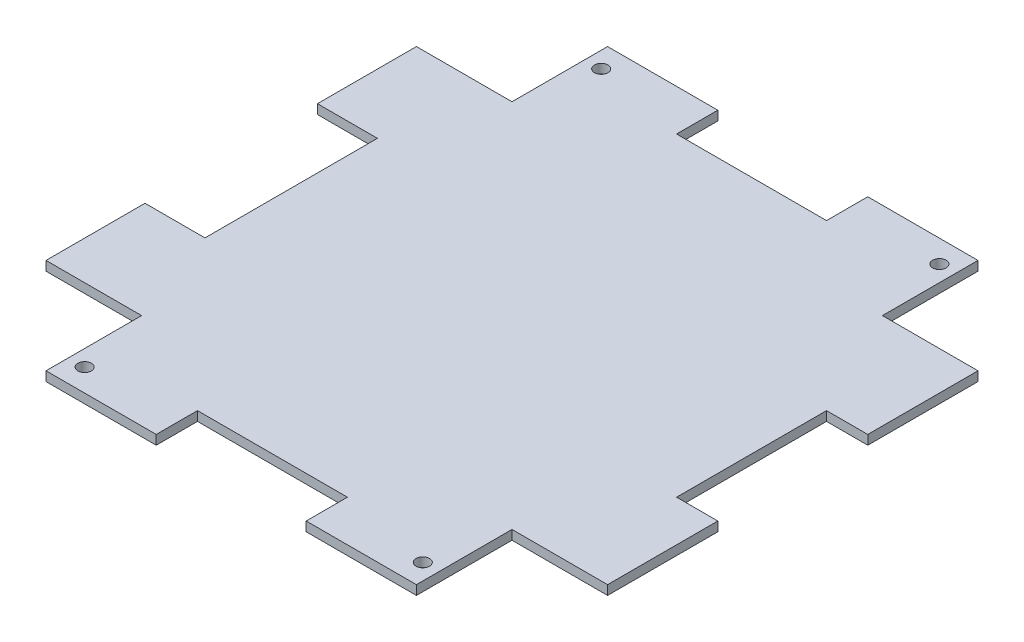
SolidWorks part; units mm, degrees
ref_plane "Front Plane" through (0, 0, 0) normal (0, 0, 1) x (1, 0, 0)
ref_plane "Top Plane" through (0, 0, 0) normal (0, 1, 0) x (1, 0, 0)
ref_plane "Right Plane" through (0, 0, 0) normal (1, 0, 0) x (0, 0, -1)
sketch "Sketch1" plane through (0, 0, 0) normal (0, 1, 0) x (1, 0, 0)
  line L0 (-62.2282, -68.317) -> (-29.8462, -68.317)
  line L1 (-29.8462, -68.317) -> (-29.8462, -100.699)
  line L2 (-29.8462, -100.699) -> (95.6398, -100.699)
  line L3 (95.6398, -100.699) -> (95.6398, -68.317)
  line L4 (95.6398, -68.317) -> (128.0218, -68.317)
  line L5 (128.0218, -68.317) -> (128.0218, 57.169)
  line L6 (128.0218, 57.169) -> (95.6398, 57.169)
  line L7 (95.6398, 57.169) -> (95.6398, 89.551)
  line L8 (95.6398, 89.551) -> (-29.8462, 89.551)
  line L9 (-29.8462, 89.551) -> (-29.8462, 57.169)
  line L10 (-29.8462, 57.169) -> (-62.2282, 57.169)
  line L11 (-62.2282, 57.169) -> (-62.2282, -68.317)
  dimension "D1" = 32.382
  dimension "D2" = 190.25
  dimension "D3" = 190.25
extrude "Boss-Extrude1" add sketch "Sketch1" along normal blind 3.175
sketch "Sketch2" plane through (0, 3.175, 0) normal (0, 1, 0) x (1, 0, 0)
  line L0 (-29.8462, -100.699) -> (95.6398, -100.699) construction
  line L1 (-29.8462, -68.317) -> (-29.8462, -100.699) construction
  line L2 (95.6398, 89.551) -> (-29.8462, 89.551) construction
  line L3 (95.6398, 57.169) -> (95.6398, 89.551) construction
  circle A0 centre (-24.3852, 81.931) radius 2.286
  circle A1 centre (90.1788, 81.931) radius 2.286
  circle A2 centre (90.1788, -93.079) radius 2.286
  circle A3 centre (-24.3852, -93.079) radius 2.286
  dimension "D1" = 4.572
  dimension "D2" = 7.62
  dimension "D3" = 5.461
  dimension "D4" = 7.62
  dimension "D5" = 5.461
extrude "Cut-Extrude1" cut sketch "Sketch2" against normal through all
sketch "Sketch3" plane through (0, 3.175, 0) normal (0, 1, 0) x (1, 0, 0)
  line L0 (-62.2282, 57.169) -> (-62.2282, -68.317) construction
  line L1 (-62.2282, -34.784) -> (-41.9082, -34.784)
  line L2 (-62.2282, -34.784) -> (-62.2282, 23.636)
  line L3 (-62.2282, 23.636) -> (-41.9082, 23.636)
  line L4 (-41.9082, -34.784) -> (-41.9082, 23.636)
  line L5 (95.6398, 89.551) -> (-29.8462, 89.551) construction
  line L6 (7.4968, 89.551) -> (58.2968, 89.551)
  line L7 (7.4968, 89.551) -> (7.4968, 75.581)
  line L8 (7.4968, 75.581) -> (58.2968, 75.581)
  line L9 (58.2968, 89.551) -> (58.2968, 75.581)
  line L10 (128.0218, -68.317) -> (128.0218, 57.169) construction
  line L11 (128.0218, 19.826) -> (114.0518, 19.826)
  line L12 (128.0218, 19.826) -> (128.0218, -30.974)
  line L13 (128.0218, -30.974) -> (114.0518, -30.974)
  line L14 (114.0518, 19.826) -> (114.0518, -30.974)
  line L15 (-29.8462, -100.699) -> (95.6398, -100.699) construction
  line L16 (58.2968, -100.699) -> (7.4968, -100.699)
  line L17 (58.2968, -100.699) -> (58.2968, -86.729)
  line L18 (58.2968, -86.729) -> (7.4968, -86.729)
  line L19 (7.4968, -100.699) -> (7.4968, -86.729)
  line L20 (95.6398, 89.551) -> (-29.8462, 89.551) construction
  line L21 (-62.2282, 57.169) -> (-62.2282, -68.317) construction
  point P26 (32.8968, 89.551)
  point P27 (32.8968, 75.581)
  point P28 (32.8968, -86.729)
  point P31 (-62.2282, -5.574)
  point P32 (-41.9082, -5.574)
  point P33 (114.0518, -5.574)
  dimension "D1" = 50.8
  dimension "D2" = 13.97
  dimension "D3" = 58.42
  dimension "D4" = 20.32
extrude "Cut-Extrude2" cut sketch "Sketch3" against normal through all
